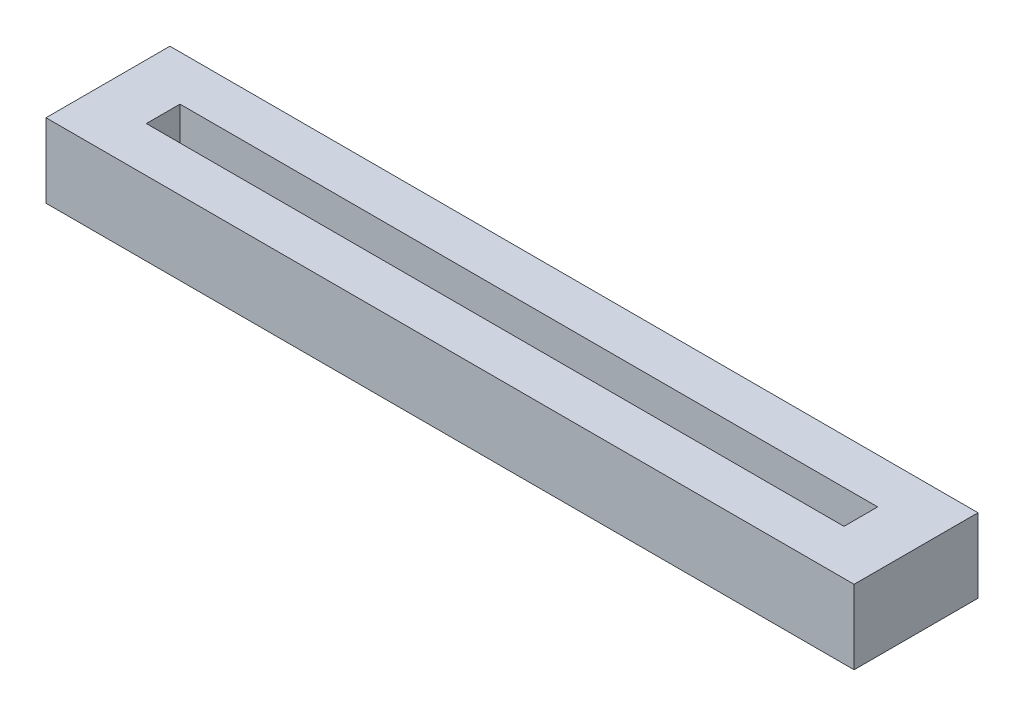
SolidWorks part; units mm, degrees
ref_plane "Спереди" through (0, 0, 0) normal (0, 0, 1) x (1, 0, 0)
ref_plane "Сверху" through (0, 0, 0) normal (0, 1, 0) x (1, 0, 0)
ref_plane "Справа" through (0, 0, 0) normal (1, 0, 0) x (0, 0, -1)
sketch "Sketch1" plane through (0, 0, 0) normal (0, 1, 0) x (1, 0, 0)
  line L1 (30, -4.6) -> (-30, -4.6)
  line L2 (30, -4.6) -> (30, 4.6)
  line L3 (30, 4.6) -> (-30, 4.6)
  line L4 (-30, -4.6) -> (-30, 4.6)
  line L5 (30, -4.6) -> (-30, 4.6) construction
  line L6 (30, 4.6) -> (-30, -4.6) construction
  point P0 (0, 0)
  dimension "D1" = 9.2
  dimension "D2" = 60
extrude "Boss-Extrude1" add sketch "Sketch1" along normal blind 5.5
sketch "Sketch2" plane through (0, 5.5, 0) normal (0, 1, 0) x (1, 0, 0)
  line L0 (-30, 0) -> (30, 0) construction
  line L1 (-30, 4.6) -> (-30, -4.6) construction
  line L2 (30, -4.6) -> (30, 4.6) construction
  line L4 (25.9, -1.25) -> (-25.9, -1.25)
  line L5 (25.9, -1.25) -> (25.9, 1.25)
  line L6 (25.9, 1.25) -> (-25.9, 1.25)
  line L7 (-25.9, -1.25) -> (-25.9, 1.25)
  line L8 (25.9, -1.25) -> (-25.9, 1.25) construction
  line L9 (25.9, 1.25) -> (-25.9, -1.25) construction
  point P6 (0, 0)
  dimension "D1" = 2.5
  dimension "D2" = 51.8
extrude "Cut-Extrude1" cut sketch "Sketch2" against normal blind 4.7
